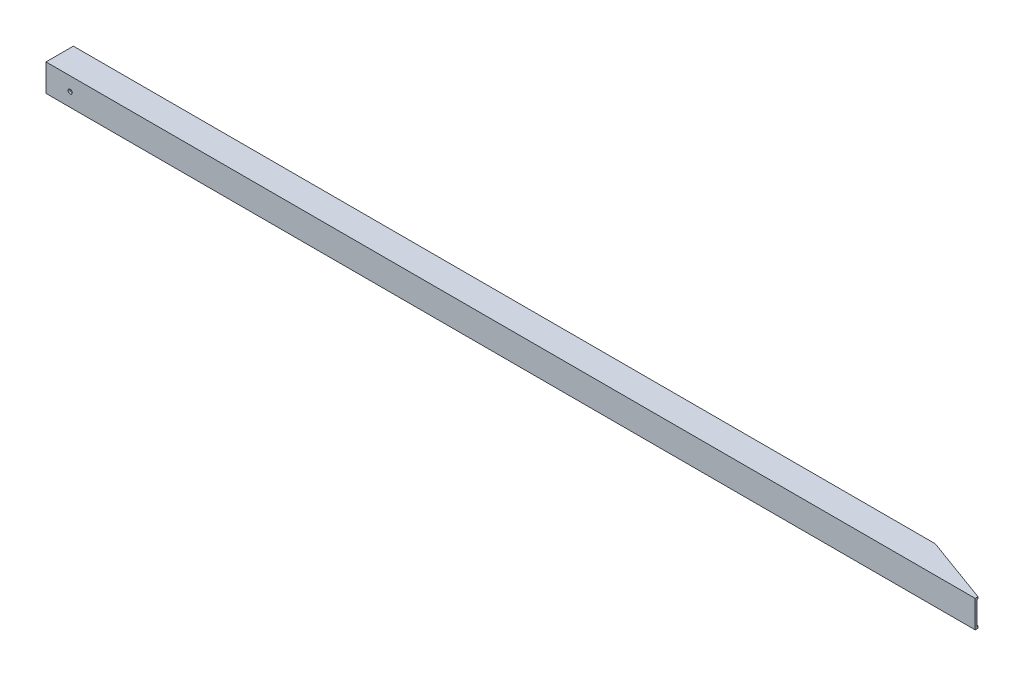
SolidWorks part; units mm, degrees
ref_plane "Front Plane" through (0, 0, 0) normal (0, 0, 1) x (1, 0, 0)
ref_plane "Top Plane" through (0, 0, 0) normal (0, 1, 0) x (1, 0, 0)
ref_plane "Right Plane" through (0, 0, 0) normal (1, 0, 0) x (0, 0, -1)
sketch "Sketch1" plane through (0, 0, 0) normal (1, 0, 0) x (0, 0, -1)
  line L0 (3.175, 3.175) -> (3.175, 41.275)
  line L1 (0, 0) -> (44.45, 0)
  line L2 (0, 0) -> (0, 44.45)
  line L3 (0, 44.45) -> (44.45, 44.45)
  line L4 (44.45, 0) -> (44.45, 44.45)
  line L5 (3.175, 41.275) -> (41.275, 41.275)
  line L6 (41.275, 3.175) -> (41.275, 41.275)
  line L7 (3.175, 3.175) -> (41.275, 3.175)
  dimension "D2" = 44.45
  dimension "D1" = 3.175
extrude "Boss-Extrude1" add sketch "Sketch1" along normal blind 1524
sketch "Sketch2" plane through (0, 44.45, 0) normal (0, 1, 0) x (1, 0, 0)
  line L0 (1524, 0) -> (1401.8746, 44.45)
  line L1 (1524, 44.45) -> (0, 44.45) construction
  line L2 (1401.8746, 44.45) -> (1524, 44.45)
  line L3 (1524, 44.45) -> (1524, 0)
  line L4 (1524, 0) -> (0, 0) construction
  dimension "D1" = 20
extrude "Cut-Extrude1" cut sketch "Sketch2" against normal through all
hole_wizard "1/4 Clearance Hole1" positions "Sketch3" profile "Sketch4" hole size "1/4" standard "ANSI Inch" end condition through all
sketch "Sketch3" plane through (0, 0, 0) normal (0, 0, 1) x (1, 0, 0)
  line L0 (0, 44.45) -> (0, 0) construction
  point P0 (39.37, 22.225)
  point P5 (0, 22.225)
  dimension "D1" = 39.37
sketch "Sketch4" plane through (39.37, 22.225, 0) normal (1, 0, 0) x (0, -1, 0)
  line L0 (0, 0) -> (0, 44.45)
  line L1 (0, 44.45) -> (3.3782, 44.45)
  line L2 (3.3782, 44.45) -> (3.3782, 0)
  line L5 (3.3782, 0) -> (0, 0)
  line L11 (0, -6.35) -> (0, 107.95) construction
  dimension "Thru Hole Dia." = 6.7564
  dimension "Thru Hole Depth" = 44.45
sketch "Sketch5" plane through (0, 44.45, 0) normal (0, 1, 0) x (1, 0, 0)
  line L0 (1524, 0) -> (1511.3, 0)
  line L1 (1524, 0) -> (0, 0) construction
  line L2 (1511.3, 0) -> (1511.3, 4.6224)
  line L3 (1401.8746, 44.45) -> (1524, 0) construction
  line L4 (1511.3, 4.6224) -> (1524, 0)
  dimension "D1" = 12.7
extrude "Cut-Extrude2" cut sketch "Sketch5" against normal through all
